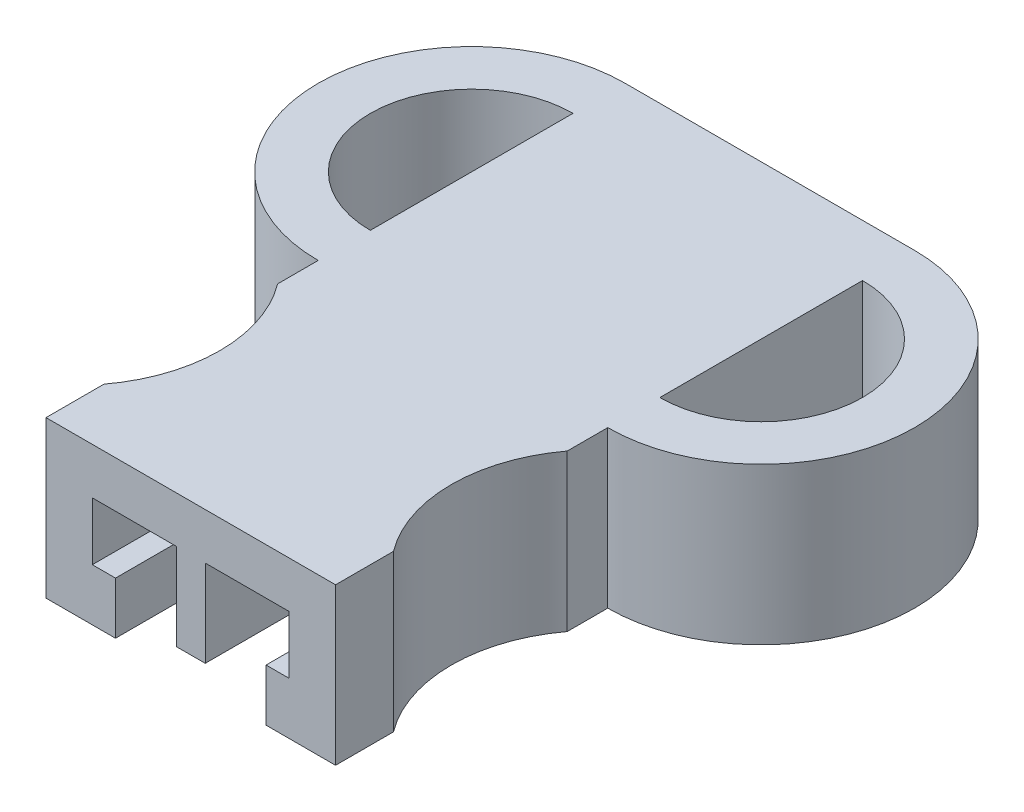
SolidWorks part; units mm, degrees
ref_plane "Front Plane" through (0, 0, 0) normal (0, 0, 1) x (1, 0, 0)
ref_plane "Top Plane" through (0, 0, 0) normal (0, 1, 0) x (1, 0, 0)
ref_plane "Right Plane" through (0, 0, 0) normal (1, 0, 0) x (0, 0, -1)
sketch "Sketch1" plane through (0, 0, 0) normal (0, 1, 0) x (1, 0, 0)
  line L0 (0, -22.86) -> (0, -25.4)
  line L1 (0, 0) -> (12.7, 0)
  line L2 (0, 0) -> (0, -15.24)
  line L3 (0, -25.4) -> (12.7, -25.4)
  line L4 (12.7, 0) -> (12.7, -15.24)
  line L5 (12.7, -22.86) -> (12.7, -25.4)
  arc A0 (0, -22.86) -> (0, -15.24) centre (-5.08, -19.05) ccw
  arc A1 (12.7, -15.24) -> (12.7, -22.86) centre (17.78, -19.05) ccw
  dimension "D1" = 12.7
  dimension "D2" = 25.4
  dimension "D3" = 6.35
  dimension "D4" = 5.08
  dimension "D5" = 5.08
  dimension "D6" = 2.54
extrude "Boss-Extrude1" add sketch "Sketch1" along normal blind 6.858
sketch "Sketch2" plane through (0, 0, 25.4) normal (0, 0, 1) x (1, 0, 0)
  line L0 (3.048, 0) -> (3.048, 2.286)
  line L1 (0, 0) -> (12.7, 0) construction
  line L2 (3.048, 2.286) -> (2.032, 2.286)
  line L3 (2.032, 2.286) -> (2.032, 4.826)
  line L4 (2.032, 4.826) -> (5.715, 4.826)
  line L5 (6.985, 4.826) -> (10.668, 4.826)
  line L6 (6.35, 1.016) -> (6.35, 0) construction
  line L7 (5.715, 4.826) -> (5.715, 1.016)
  line L8 (5.715, 1.016) -> (6.985, 1.016)
  line L9 (10.668, 4.826) -> (10.668, 2.286)
  line L10 (10.668, 2.286) -> (9.652, 2.286)
  line L11 (9.652, 2.286) -> (9.652, 0)
  line L12 (3.048, 0) -> (9.652, 0)
  line L13 (0, 6.858) -> (0, 0) construction
  line L15 (3.048, 0) -> (0, 0) construction
  line L16 (9.652, 0) -> (12.7, 0) construction
  line L17 (6.985, 4.826) -> (6.985, 1.016)
  line L19 (12.7, 6.858) -> (12.7, 0) construction
  dimension "D1" = 3.048
  dimension "D2" = 1.27
  dimension "D3" = 3.81
  dimension "D4" = 2.54
  dimension "D5" = 2.286
  dimension "D6" = 2.032
extrude "Cut-Extrude1" cut sketch "Sketch2" against normal through all
sketch "Sketch5" plane through (0, 6.858, 0) normal (0, 1, 0) x (1, 0, 0)
  line L0 (0, 0) -> (0, -15.24) construction
  line L1 (12.7, -15.24) -> (12.7, 0) construction
  line L2 (0, 0) -> (0, -2.286)
  line L3 (12.7, -13.462) -> (12.7, -11.176)
  line L4 (12.7, -2.286) -> (12.7, 0)
  line L5 (0, -11.176) -> (0, -13.462)
  arc A0 (0, -2.286) -> (0, -11.176) centre (0, -6.731) ccw
  arc A1 (0, 0) -> (0, -13.462) centre (0, -6.731) ccw
  arc A2 (12.7, -11.176) -> (12.7, -2.286) centre (12.7, -6.731) ccw
  arc A3 (12.7, -13.462) -> (12.7, 0) centre (12.7, -6.731) ccw
  dimension "D1" = 2.286
  dimension "D2" = 8.89
extrude "Boss-Extrude2" add sketch "Sketch5" against normal through all
sketch "Sketch6" plane through (0, 0, 0) normal (0, 0, -1) x (-1, 0, 0)
  line L0 (-10.668, 4.826) -> (-6.985, 4.826) construction
  line L1 (-6.985, 1.016) -> (-5.715, 1.016)
  line L2 (-6.985, 1.016) -> (-6.985, 4.826)
  line L3 (-6.985, 4.826) -> (-5.715, 4.826)
  line L4 (-5.715, 1.016) -> (-5.715, 4.826)
  line L5 (-5.715, 1.016) -> (-5.715, 4.826) construction
extrude "Cut-Extrude2" cut sketch "Sketch6" against normal blind 6.35
